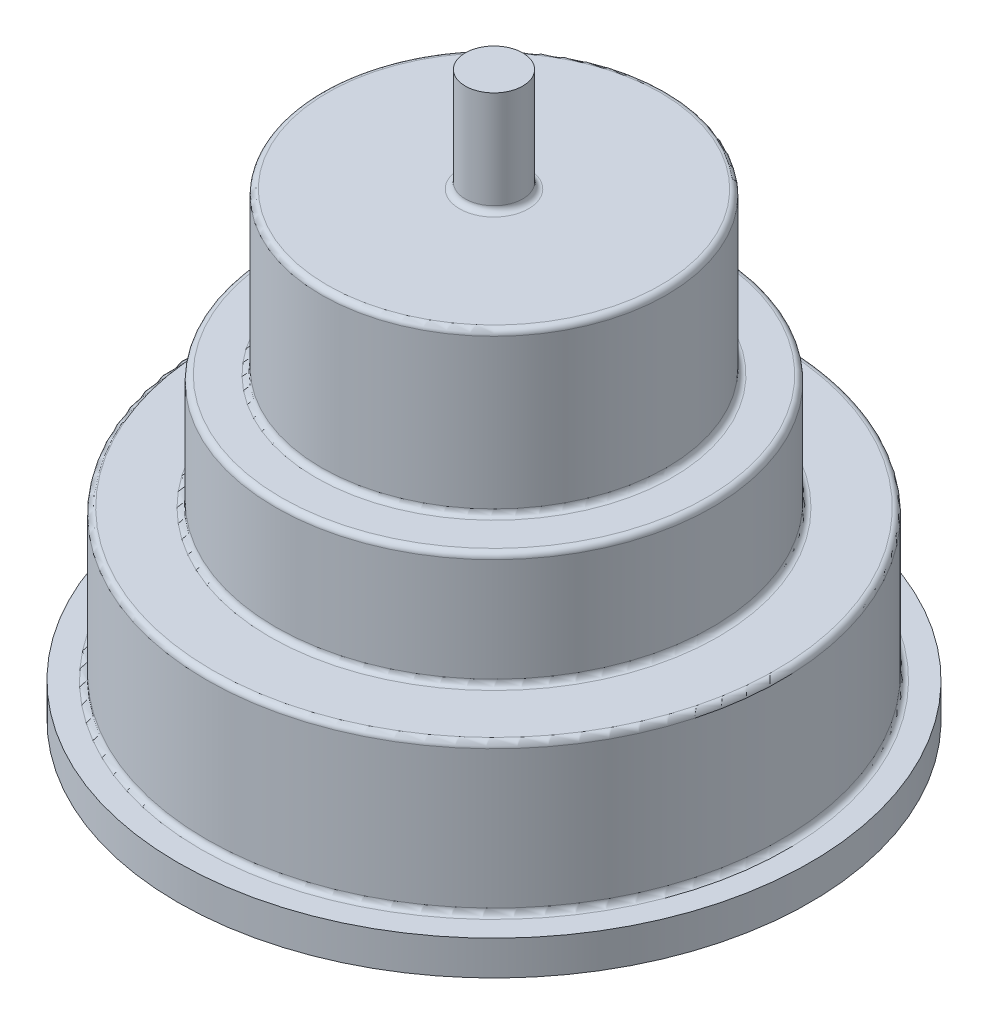
SolidWorks part; units mm, degrees
material "Plain Carbon Steel"
ref_plane "Front Plane" through (0, 0, 0) normal (0, 0, 1) x (1, 0, 0)
ref_plane "Top Plane" through (0, 0, 0) normal (0, 1, 0) x (1, 0, 0)
ref_plane "Right Plane" through (0, 0, 0) normal (1, 0, 0) x (0, 0, -1)
sketch "Sketch1" plane through (0, 0, 0) normal (0, 1, 0) x (1, 0, 0)
  circle A0 centre (0, 0) radius 27.5
  dimension "D1" = 55
extrude "Boss-Extrude1" add sketch "Sketch1" along normal blind 3
sketch "Sketch2" plane through (0, 3, 0) normal (0, 1, 0) x (1, 0, 0)
  circle A0 centre (0, 0) radius 25
  dimension "D1" = 50
extrude "Boss-Extrude2" add sketch "Sketch2" along normal blind 23
sketch "Sketch7" plane through (0, 26, 0) normal (0, 1, 0) x (1, 0, 0)
  circle A0 centre (0, 0) radius 15
  dimension "D1" = 30
extrude "Boss-Extrude4" add sketch "Sketch7" along normal blind 14
sketch "Sketch3" plane through (0, 40, 0) normal (0, 1, 0) x (1, 0, 0)
  circle A0 centre (0, 0) radius 2.5
  dimension "D1" = 5
extrude "Boss-Extrude3" add sketch "Sketch3" along normal blind 9
hole_wizard "M4 Tapped Hole1" positions "Sketch5" profile "Sketch4" tap size "M4" standard "ISO"
sketch "Sketch5" plane through (0, 0, 0) normal (0, -1, 0) x (-1, 0, 0)
  point P2 (0, -17)
  point P12 (-17, 0)
  point P13 (0, 17)
  point P14 (17, 0)
  dimension "D1" = 17
  dimension "D2" = 4
sketch "Sketch4" plane through (0, 0, 17) normal (1, 0, 0) x (0, 0, -1)
  line L0 (0, 0) -> (0, 11.9914)
  line L1 (0, 11.9914) -> (1.65, 11)
  line L2 (1.65, 11) -> (1.65, 0)
  line L5 (1.65, 0) -> (0, 0)
  line L10 (0, 11.9914) -> (-1.65, 11) construction
  line L11 (0, -6.35) -> (0, 107.95) construction
  dimension "Tap Drill Dia." = 3.3
  dimension "Tap Drill Depth" = 11
  dimension "Drill Angle" = 118
cosmetic thread "Hole Thread1" parameters "D1"=11, "D2"=4
cosmetic thread "Hole Thread2" parameters "D1"=11, "D2"=4
cosmetic thread "Hole Thread3" parameters "D1"=11, "D2"=4
cosmetic thread "Hole Thread4" parameters "D1"=11, "D2"=4
sketch "Sketch6" plane through (0, 49, 0) normal (0, 1, 0) x (1, 0, 0)
  circle A0 centre (0, 0) radius 2.5
  dimension "D1" = 5
extrude "Cut-Extrude1" [suppressed] cut sketch "Sketch6" against normal blind 10
sketch "Sketch8" plane through (0, 26, 0) normal (0, 1, 0) x (1, 0, 0)
  circle A0 centre (0, 0) radius 25
  circle A1 centre (0, 0) radius 19
  dimension "D1" = 38
extrude "Cut-Extrude2" cut sketch "Sketch8" against normal offset from surface (10 mm away) 13 up to face at (0, 3, 25)
fillet "Fillet2" radius 0.5 7 edges at (0, 26, 15) (0, 40, 2.5) (0, 3, 25) (0, 40, 15) (0, 26, 19) (0, 16, 25) (0, 16, 19)
